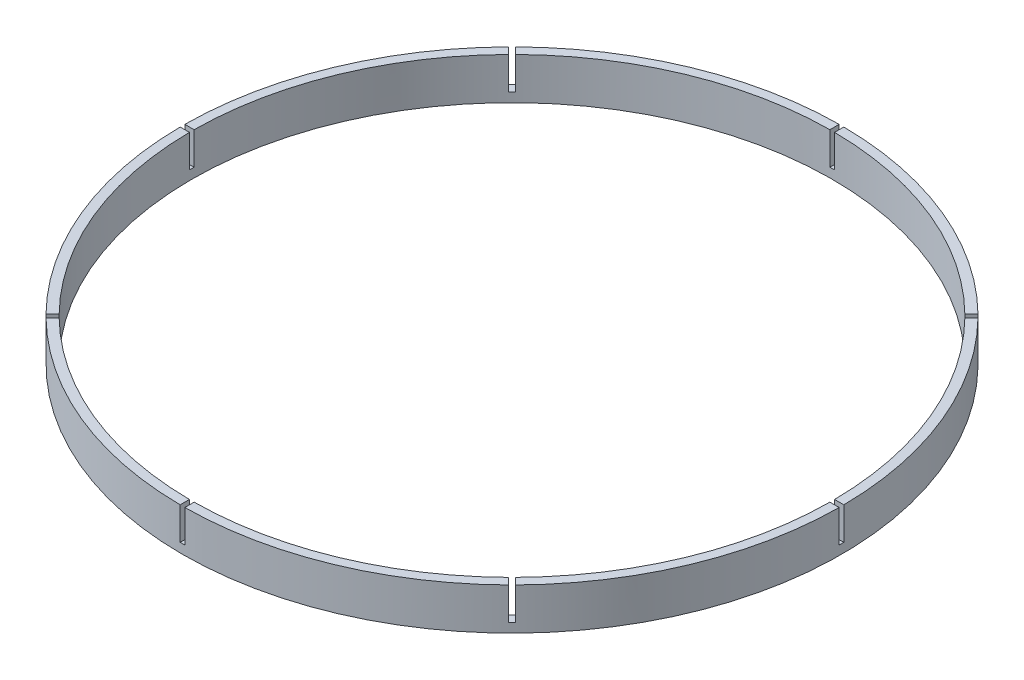
SolidWorks part; units mm, degrees
ref_plane "Front Plane" through (0, 0, 0) normal (0, 0, 1) x (1, 0, 0)
ref_plane "Top Plane" through (0, 0, 0) normal (0, 1, 0) x (1, 0, 0)
ref_plane "Right Plane" through (0, 0, 0) normal (1, 0, 0) x (0, 0, -1)
sketch "Sketch1" plane through (0, 0, 0) normal (0, 1, 0) x (1, 0, 0)
  circle A2 centre (0, 0) radius 70 construction
  circle A3 centre (0, 0) radius 71
  circle A4 centre (0, 0) radius 69
  dimension "D1" = 140
  dimension "D2" = 1
  dimension "D3" = 1
extrude "Boss-Extrude1" add sketch "Sketch1" along normal blind 9
sketch "Sketch2" plane through (0, 9, 0) normal (0, 1, 0) x (1, 0, 0)
  line L0 (0, 0) -> (0, 71) construction
  line L1 (0.5, 68.9982) -> (0.5, 70.9982)
  line L2 (-0.5, 68.9982) -> (-0.5, 70.9982)
  line L3 (0.5, 0) -> (0.5, 71) construction
  line L4 (-0.5, 0) -> (-0.5, 71) construction
  circle A0 centre (0, 0) radius 71 construction
  arc A1 (0.5, 70.9982) -> (-0.5, 70.9982) centre (0, 0) ccw
  circle A2 centre (0, 0) radius 69 construction
  arc A3 (0.5, 68.9982) -> (-0.5, 68.9982) centre (0, 0) ccw
  dimension "D1" = 0.5
  dimension "D2" = 0.5
extrude "Cut-Extrude1" cut sketch "Sketch2" against normal offset from surface (7 mm away) 2 up to face at (0, 0, 71)
pattern_circular "CirPattern1" count 8 over 360 about axis through (0, 0, 0) along (0, 1, 0) of "Cut-Extrude1"
